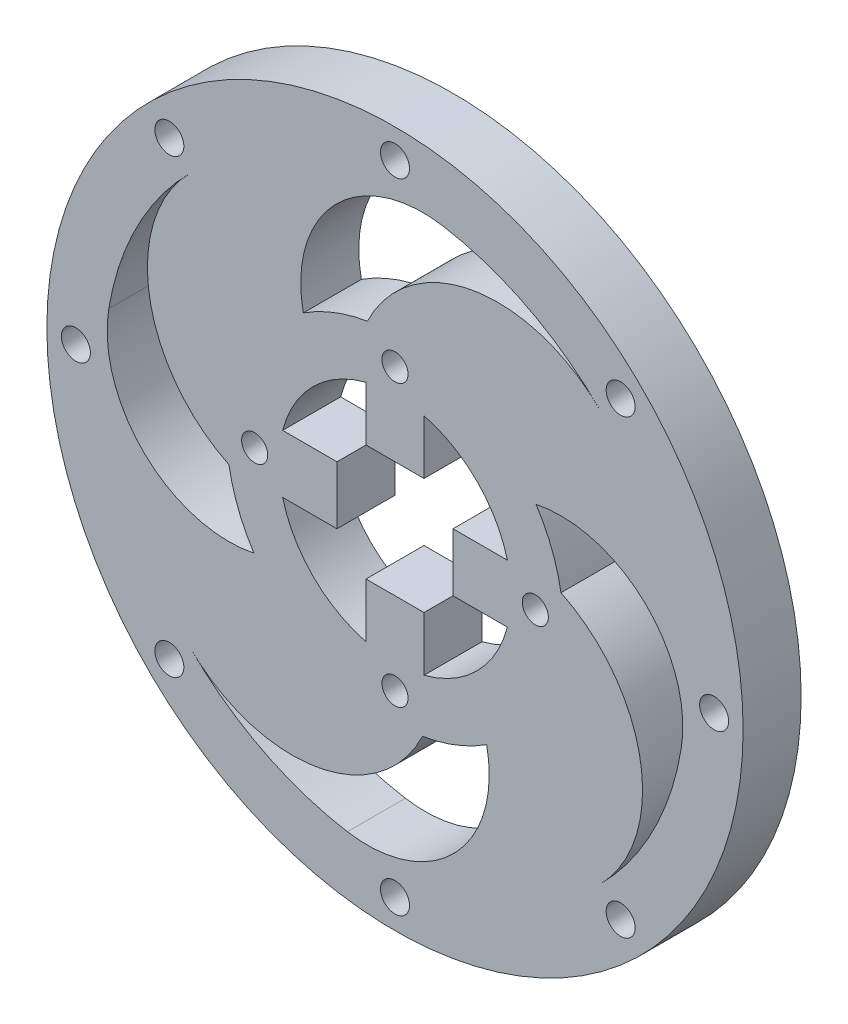
SolidWorks part; units mm, degrees
ref_plane "Front Plane" through (0, 0, 0) normal (0, 0, 1) x (1, 0, 0)
ref_plane "Top Plane" through (0, 0, 0) normal (0, 1, 0) x (1, 0, 0)
ref_plane "Right Plane" through (0, 0, 0) normal (1, 0, 0) x (0, 0, -1)
sketch "Sketch6" plane through (0, 0, 0) normal (0, 0, 1) x (1, 0, 0)
  circle A0 centre (0, 0) radius 20
  circle A1 centre (0, 0) radius 29
  dimension "D1" = 40
  dimension "D2" = 58
extrude "Inner Ring" add sketch "Sketch6" against normal blind 10 separate body
sketch "Sketch7" plane through (0, 0, 0) normal (0, 0, 1) x (1, 0, 0)
  line L2 (-10, 5) -> (-10, -5)
  line L3 (-5, 10) -> (5, 10)
  line L4 (10, 5) -> (10, -5)
  line L5 (-5, -10) -> (5, -10)
  line L14 (-19.3649, 5) -> (-10, 5)
  line L15 (-19.3649, -5) -> (-10, -5)
  line L16 (-5, 19.3649) -> (-5, 10)
  line L17 (5, 19.3649) -> (5, 10)
  line L18 (19.3649, 5) -> (10, 5)
  line L19 (19.3649, -5) -> (10, -5)
  line L20 (5, -19.3649) -> (5, -10)
  line L21 (-5, -19.3649) -> (-5, -10)
  circle A1 centre (0, 0) radius 20
  circle M19 centre (0, 0) radius 20
  dimension "D1" = 20
  dimension "D2" = 20
  dimension "D3" = 10
  dimension "D5" = 10
  dimension "D7" = 10
  dimension "D8" = 10
extrude "Motor Connector Cut" add sketch "Sketch7" against normal blind 10 contours L19 L18 L4 M19 | L17 L16 L3 M19 | L15 L2 L14 M19 | L21 L20 L5 M19
sketch "Sketch8" plane through (0, 0, 0) normal (0, 0, 1) x (1, 0, 0)
  circle A1 centre (0, 24.1825) radius 2.25
  circle A2 centre (24.1825, 0) radius 2.25
  circle A3 centre (0, -24.1825) radius 2.25
  circle A4 centre (-24.1825, 0) radius 2.25
  dimension "D1" = 4.5
  dimension "D2" = 4.5
  dimension "D3" = 4.5
  dimension "D4" = 4.5
  dimension "D6" = 48.3649
  dimension "D8" = 48.3649
extrude "Motor Connector Holes" cut sketch "Sketch8" against normal blind 18 and the other way blind 1
sketch "Sketch9" plane through (0, 0, 0) normal (0, 0, 1) x (1, 0, 0)
  circle A0 centre (0, 0) radius 50
  circle A1 centre (0, 0) radius 60
  circle A2 centre (0, 55) radius 2.5
  circle A3 centre (0, 55) radius 1.5
  circle A4 centre (-38.8909, 38.8909) radius 1.5
  circle A5 centre (-55, 0) radius 1.5
  circle A6 centre (-38.8909, -38.8909) radius 1.5
  circle A7 centre (0, -55) radius 1.5
  circle A8 centre (38.8909, -38.8909) radius 1.5
  circle A9 centre (55, 0) radius 1.5
  circle A10 centre (38.8909, 38.8909) radius 1.5
  circle A11 centre (-38.8909, 38.8909) radius 2.5
  circle A12 centre (-55, 0) radius 2.5
  circle A13 centre (-38.8909, -38.8909) radius 2.5
  circle A14 centre (0, -55) radius 2.5
  circle A15 centre (38.8909, -38.8909) radius 2.5
  circle A16 centre (55, 0) radius 2.5
  circle A17 centre (38.8909, 38.8909) radius 2.5
  dimension "D1" = 120
  dimension "D2" = 100
  dimension "D3" = 3
  dimension "D4" = 3
  dimension "D5" = 3
  dimension "D6" = 3
  dimension "D7" = 3
  dimension "D8" = 3
  dimension "D9" = 3
  dimension "D10" = 3
  dimension "D11" = 5
  dimension "D12" = 5
  dimension "D13" = 5
  dimension "D14" = 5
  dimension "D15" = 5
  dimension "D16" = 5
  dimension "D17" = 5
  dimension "D18" = 5
sketch "Sketch10" plane through (0, 0, 0) normal (0, 0, 1) x (1, 0, 0)
  circle A0 centre (0, 0) radius 29
  circle A1 centre (0, 29) radius 21
  circle A2 centre (29, 0) radius 21
  circle A3 centre (0, -29) radius 21
  circle A4 centre (-29, 0) radius 21
  circle A5 centre (0, 0) radius 50
  circle A6 centre (-17.7016, 17.7016) radius 24.9662
  circle A7 centre (17.7016, 17.7016) radius 24.9662
  circle A8 centre (17.7016, -17.7016) radius 24.9662
  circle A9 centre (-17.7016, -17.7016) radius 24.9662
  circle A10 centre (-28.6072, 4.7568) radius 21
  circle A11 centre (-28.6072, -4.7568) radius 21
  circle A12 centre (-4.7568, -28.6072) radius 21
  circle A13 centre (4.7568, -28.6072) radius 21
  circle A14 centre (28.6072, -4.7568) radius 21
  circle A15 centre (28.6072, 4.7568) radius 21
  circle A16 centre (4.7568, 28.6072) radius 21
  circle A17 centre (-4.7568, 28.6072) radius 21
extrude "Middle Pattern" add sketch "Sketch10" against normal blind 10 contours A0 A10 A1 | A16 A6 A1 A10 A0 | A10 A17 A4 A0 A1 | A6 A17 A10 A1 | A1 A17 A6 | A16 A17 A1 A6 | A17 A16 A1 | A16 A5 A1 | A2 A16 A15 A1 A0 | A0 A16 A2 | A16 A0 A14 A7 A2 | A16 A2 A7 A15 | A15 A7 A2 | A14 A15 A2 A7 | A15 A14 A2 | A1 A15 A0 | A2 A13 A0 | A3 A14 A13 A2 A0 | A0 A14 A3 | A14 A0 A12 A8 A3 | A14 A3 A8 A13 | A12 A13 A3 A8 | A3 A13 A8 | A13 A12 A3 | A13 A3 A5 | A15 A2 A5 | A17 A1 A5 | A12 A0 A10 A9 A4 | A4 A12 A11 A3 A0 | A0 A12 A4 | A12 A4 A9 A11 | A4 A11 A9 | A10 A11 A4 A9 | A11 A4 A5 | A11 A10 A4 | A4 A17 A0 | A0 A17 A7 A6 | A17 A0 A15 A1 A7 | A15 A16 A7 A1 | A16 A15 A7 | A15 A5 A7 | A0 A15 A8 A7 | A15 A0 A13 A2 A8 | A13 A14 A8 A2 | A14 A13 A8 | A7 A8 A0 | A6 A7 A0 | A13 A5 A8 | A11 A5 A9 | A12 A11 A9 | A11 A12 A9 A3 | A13 A0 A11 A3 A9 | A0 A13 A9 A8 | A3 A11 A0 | A8 A9 A0 | A17 A4 A6 A11 A0 | A17 A10 A6 A4 | A17 A6 A10 | A0 A11 A6 A9 | A0 A9 A6 | A17 A5 A6 | A12 A5 A3 | A10 A5 A4 | A14 A5 A2
extrude "Boss-Extrude1" add sketch "Sketch9" against normal blind 10 contours A1 A17 A16 A15 A14 A13 A12 A11 A2 A0 | A3 | A10
